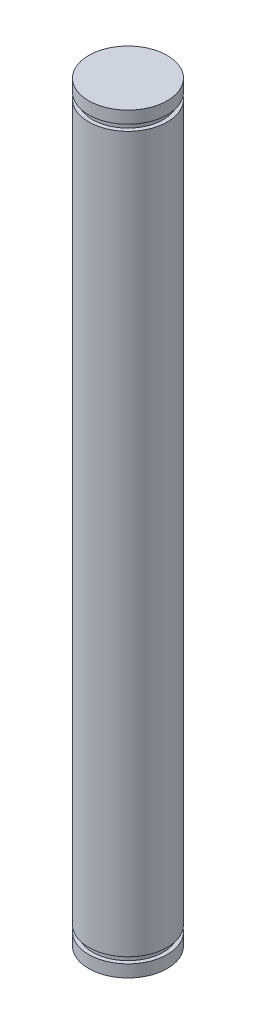
SolidWorks part; units mm, degrees
material "AISI 1045 Steel, cold drawn"
ref_plane "Front Plane" through (0, 0, 0) normal (0, 0, 1) x (1, 0, 0)
ref_plane "Top Plane" through (0, 0, 0) normal (0, 1, 0) x (1, 0, 0)
ref_plane "Right Plane" through (0, 0, 0) normal (1, 0, 0) x (0, 0, -1)
sketch "Sketch1" plane through (0, 0, 0) normal (0, 1, 0) x (1, 0, 0)
  circle A0 centre (0, 0) radius 6.35
  circle A1 centre (0, 0) radius 3.175
  dimension "D1" = 6.35
  dimension "D2" = 12.7
extrude "Boss-Extrude1" add sketch "Sketch1" along normal mid plane 119.38 contours A0 A1 | A1
sketch "Sketch2" plane through (0, -59.69, 0) normal (0, 1, 0) x (1, 0, 0)
  circle A0 centre (0, 0) radius 6.35 construction
  circle A1 centre (0, 0) radius 6.35
  circle A3 centre (0, 0) radius 5.715
  dimension "D1" = 0.635
extrude "Cut-Extrude1" cut sketch "Sketch2" against normal blind 0.9906 from offset 1.905
mirror "Mirror1" about plane through (0, 0, 0) normal (0, 1, 0) of "Cut-Extrude1"
sketch "Sketch3" plane through (0, 59.69, 0) normal (0, 1, 0) x (1, 0, 0)
  circle A0 centre (0, 0) radius 6.35
extrude "Boss-Extrude2" add sketch "Sketch3" along normal blind 1.0645
mirror "Mirror2" about plane through (0, 0, 0) normal (0, 1, 0) of "Boss-Extrude2"
